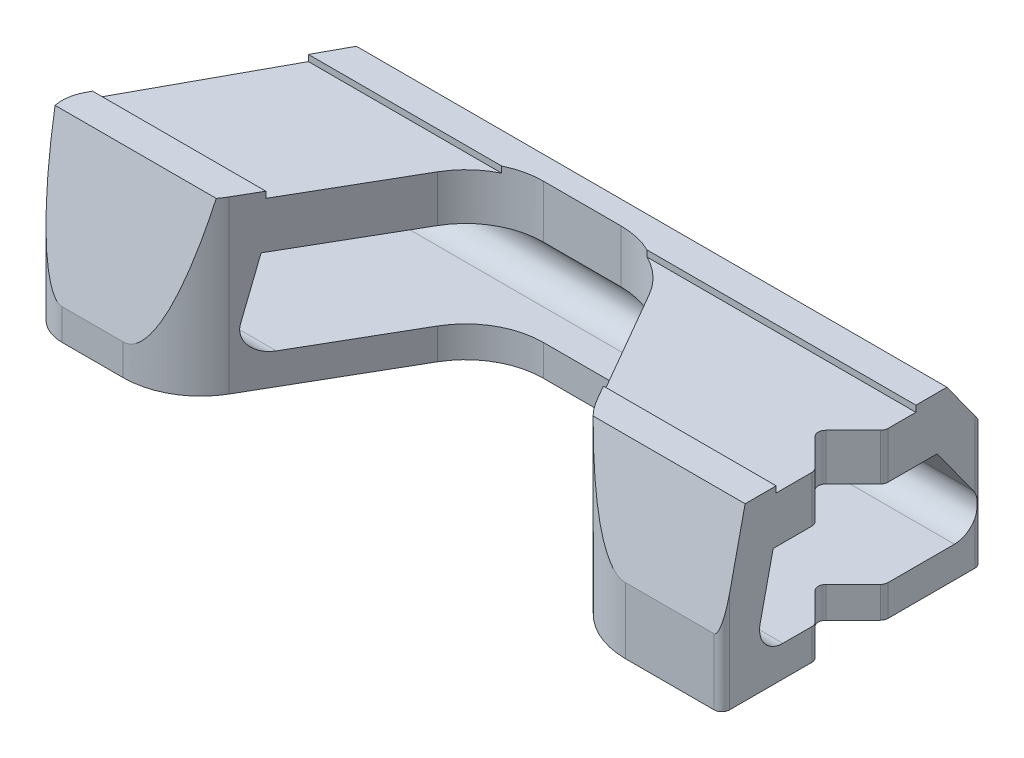
SolidWorks part; units mm, degrees
ref_plane "Front Plane" through (0, 0, 0) normal (0, 0, 1) x (1, 0, 0)
ref_plane "Top Plane" through (0, 0, 0) normal (0, 1, 0) x (1, 0, 0)
ref_plane "Right Plane" through (0, 0, 0) normal (1, 0, 0) x (0, 0, -1)
sketch "Sketch1" plane through (0, 0, 0) normal (0, 1, 0) x (1, 0, 0)
  line L0 (35, 26) -> (25, 26)
  line L1 (-15, 26) -> (-25, 26)
  line L2 (44, 17) -> (44, 5)
  line L3 (-44, -26) -> (44, -26) construction
  line L4 (-44, -26) -> (-44, 26) construction
  line L5 (-44, 26) -> (44, 26) construction
  line L6 (44, -26) -> (44, 26) construction
  line L7 (0, 26) -> (0, -26) construction
  line L8 (-44, 0) -> (44, 0) construction
  line L9 (44, -4) -> (44, -16)
  line L10 (44, 17) -> (35, 26)
  line L11 (44, 5) -> (39.5, 0.5)
  line L12 (39.5, 0.5) -> (44, -4)
  line L13 (-15, 26) -> (5, 20.641)
  line L14 (5, 20.641) -> (25, 26)
  line L15 (-25, 26) -> (-44.3911, -9.6088)
  line L16 (-5, 0) -> (5, 0) construction
  line L17 (-5, 10) -> (5, 10)
  line L18 (-5, -10) -> (5, -10)
  line L19 (-40, -17) -> (-26.362, -17)
  line L20 (44, -16) -> (25.7846, -16)
  line L21 (25.7846, -16) -> (13.6603, 5)
  line L22 (-26.362, -17) -> (-13.6603, 5)
  circle A0 centre (-40, -12) radius 5
  arc A1 (-5, 10) -> (-5, -10) centre (-5, 0) ccw
  arc A2 (5, -10) -> (5, 10) centre (5, 0) ccw
  point P4 (0, 0)
  point P20 (0, 0)
  point P31 (-26.9274, -18)
  point P32 (-25.7846, -16)
  point P33 (-25.7846, -16)
  point P34 (-19.3654, -18)
  dimension "D12" = 10
  dimension "D1" = 26
  dimension "D2" = 44
  dimension "D3" = 10
  dimension "D4" = 10
  dimension "D5" = 40
  dimension "D6" = 9
  dimension "D7" = 12
  dimension "D8" = 12
  dimension "D9" = 9
  dimension "D10" = 9
  dimension "D11" = 15
  dimension "D13" = 40
  dimension "D14" = 12
  dimension "D15" = 20
  dimension "D16" = 10
  dimension "D17" = 60
  dimension "D18" = 60
extrude "Boss-Extrude1" add sketch "Sketch1" along normal blind 22
sketch "Sketch2" plane through (0, 22, 0) normal (0, 1, 0) x (1, 0, 0)
  line L1 (-60, -9) -> (60, -9)
  line L2 (-60, -9) -> (-60, 9)
  line L3 (-60, 9) -> (60, 9)
  line L4 (60, -9) -> (60, 9)
  line L5 (0, 9) -> (0, -9) construction
  line L6 (-60, 0) -> (60, 0) construction
  point P0 (0, 0)
  dimension "D1" = 18
  dimension "D2" = 120
extrude "Cut-Extrude1" [suppressed] cut sketch "Sketch2" against normal blind 0.8
sketch "Sketch3" plane through (0, 0, 0) normal (1, 0, 0) x (0, 0, -1)
  line L0 (17, 22) -> (5, 22) construction
  line L1 (-9, 31.2) -> (9, 31.2)
  line L2 (-9, 31.2) -> (-9, 21.2)
  line L3 (-9, 21.2) -> (9, 21.2)
  line L4 (9, 31.2) -> (9, 21.2)
  line L5 (0, 21.2) -> (0, 31.2) construction
  line L6 (-9, 26.2) -> (9, 26.2) construction
  line L7 (-1001.4629, 4) -> (48998.5371, 4) construction
  line L8 (-13, 22) -> (-17, 4)
  line L9 (-4, 22) -> (-16, 22) construction
  line L10 (-17, 22) -> (-17, 0) construction
  line L11 (-17, 4) -> (-17, 31.2)
  line L12 (-17, 31.2) -> (-9, 31.2)
  line L13 (9, 31.2) -> (26, 31.2)
  line L14 (26, 31.2) -> (26, 4)
  line L15 (26, 22) -> (26, 0) construction
  line L16 (26, 4) -> (13, 22)
  line L17 (13, 22) -> (9, 22)
  line L18 (-13, 22) -> (-9, 22)
  line L19 (-9.3891, 15.2) -> (-11.0667, 7.6508)
  line L20 (11.7434, 15.2) -> (-9.3891, 15.2)
  line L21 (16.3971, 8.7565) -> (11.7434, 15.2)
  line L23 (-8.1382, 4) -> (13.9651, 4)
  line L24 (-8.1191, 20.9153) -> (-12.1191, 2.9153) construction
  line L25 (21.9466, 1.0725) -> (8.9466, 19.0725) construction
  arc A2 (-8.1382, 4) -> (-11.0667, 7.6508) centre (-8.1382, 7) cw
  arc A3 (13.9651, 4) -> (16.3971, 8.7565) centre (13.9651, 7) ccw
  point P0 (0, 26.2)
  point P24 (21.0006, 4)
  point P28 (-1001.4629, 9)
  point P29 (48998.5371, 9)
  point P33 (18.279, 6.1508)
  point P34 (22.1811, 4)
  point P36 (19.8427, 4)
  point P37 (-13, 4)
  point P38 (-12.5677, 4)
  point P40 (-11.878, 4)
  point P43 (19.8323, 4)
  dimension "D8" = 3
  dimension "D9" = 3
  dimension "D1" = 18
  dimension "D2" = 0.8
  dimension "D3" = 10
  dimension "D4" = 4
  dimension "D5" = 4
  dimension "D6" = 5
  dimension "D7" = 6
fillet "Fillet1" radius 1 9 edges at (39.5, 11, -0.5) (-25, 11, -26) (-15, 11, -26) (25, 11, -26) (35, 11, -26) (44, 11, -17) (44, 11, 4) (44, 11, 16) (44, 11, -5)
fillet "Fillet2" radius 10 3 edges at (5, 11, -20.641) (25.7846, 11, 16) (-26.362, 11, 17)
extrude "Cut-Extrude2" cut sketch "Sketch3" against normal through all both and the other way through all
